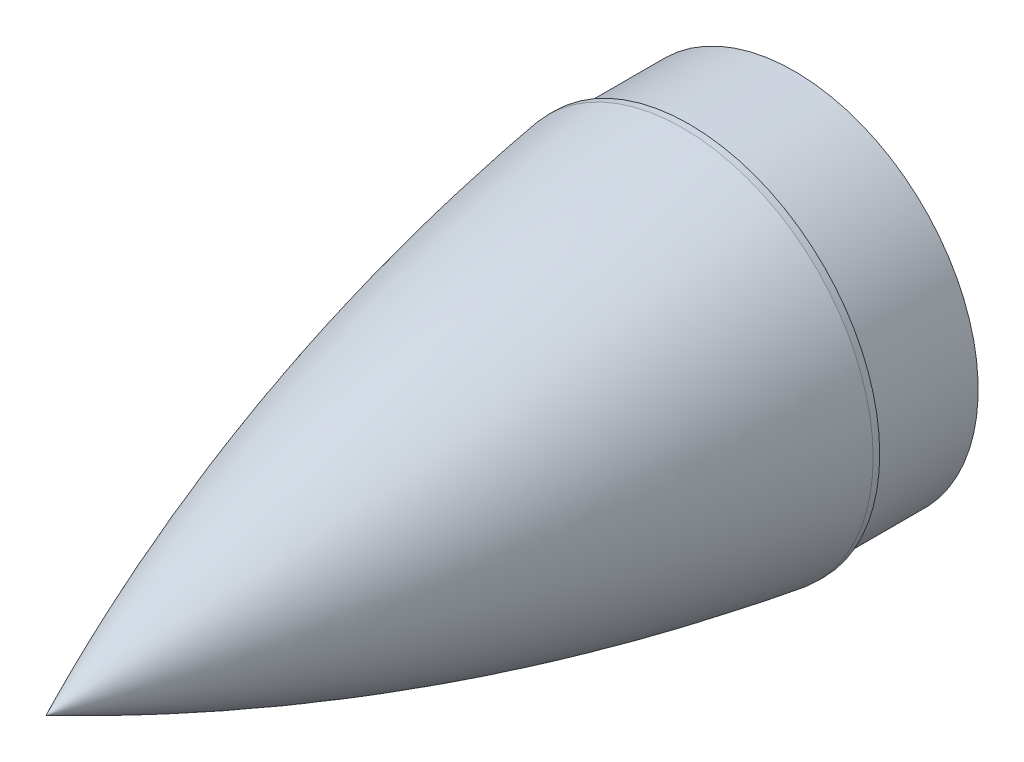
SolidWorks part; units mm, degrees
ref_plane "Front Plane" through (0, 0, 0) normal (0, 0, 1) x (1, 0, 0)
ref_plane "Top Plane" through (0, 0, 0) normal (0, 1, 0) x (1, 0, 0)
ref_plane "Right Plane" through (0, 0, 0) normal (1, 0, 0) x (0, 0, -1)
sketch "Sketch1" plane through (0, 0, 0) normal (0, 0, 1) x (1, 0, 0)
  circle A0 centre (0, 0) radius 92.075
  dimension "D1" = 184.15
extrude "Boss-Extrude1" add sketch "Sketch1" against normal blind 3.175
sketch "Sketch2" plane through (0, 0, -3.175) normal (0, 0, -1) x (-1, 0, 0)
  circle A0 centre (0, 0) radius 88.9
  dimension "D1" = 177.8
extrude "Boss-Extrude2" add sketch "Sketch2" along normal blind 50.8
sketch "Sketch3" plane through (0, 0, -53.975) normal (0, 0, -1) x (-1, 0, 0)
  circle A0 centre (0, 0) radius 85.725
  dimension "D1" = 171.45
extrude "Cut-Extrude1" cut sketch "Sketch3" against normal blind 50.8
sketch "Sketch4" plane through (0, 0, 0) normal (0, 1, 0) x (1, 0, 0)
  line L1 (0, 0) -> (0, -304.8)
  line L2 (0, -304.8) -> (0, -307.975)
  line L3 (88.9, 0) -> (92.075, 0)
  spline S0 degree 2 poles (0, -307.975) (68.5383, -160.143) (92.075, 0) knots 0 0 0 1 1 1
  spline S1 degree 2 poles (0, -304.8) (65.2775, -157.9943) (88.9, 0) knots 0 0 0 1 1 1
  dimension "D1" = 304.8
  dimension "D3" = 3.175
  dimension "D4" = 3.175
  dimension "D5" = 3.175
revolve "Revolve1" add sketch "Sketch4" angle 360 about L1
